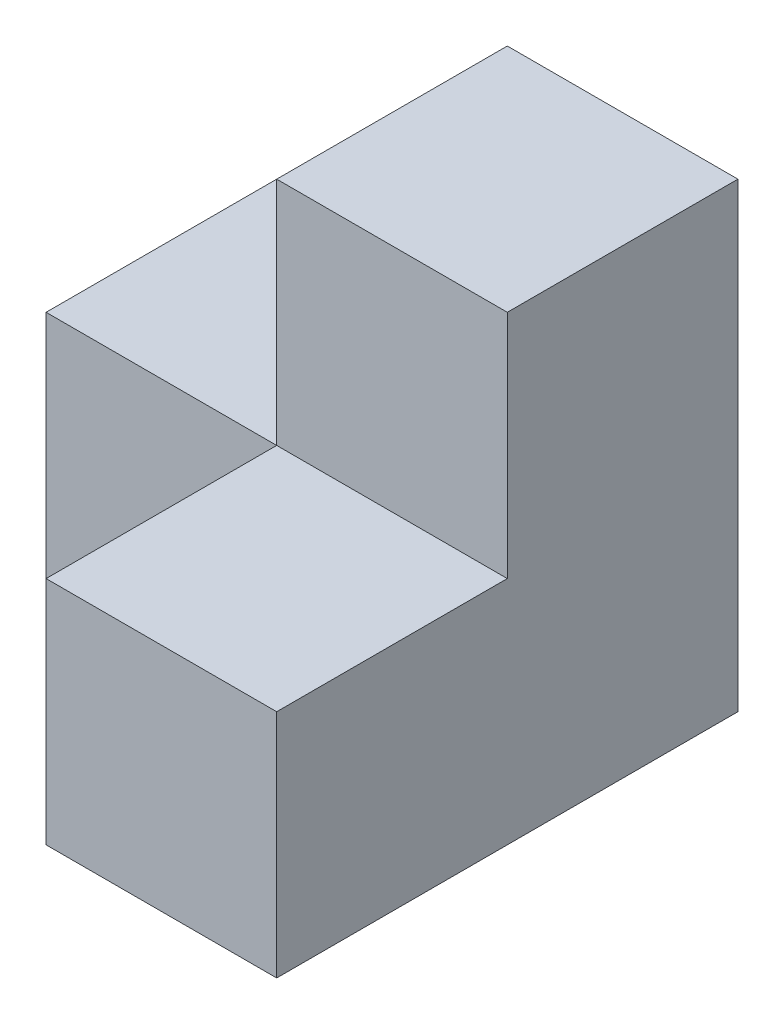
SolidWorks part; units mm, degrees
ref_plane "Front Plane" through (0, 0, 0) normal (0, 0, 1) x (1, 0, 0)
ref_plane "Top Plane" through (0, 0, 0) normal (0, 1, 0) x (1, 0, 0)
ref_plane "Right Plane" through (0, 0, 0) normal (1, 0, 0) x (0, 0, -1)
sketch "Sketch1" plane through (0, 0, 0) normal (0, 1, 0) x (1, 0, 0)
  line L1 (-25.4, -25.4) -> (25.4, -25.4)
  line L2 (-25.4, -25.4) -> (-25.4, 25.4)
  line L3 (-25.4, 25.4) -> (25.4, 25.4)
  line L4 (25.4, -25.4) -> (25.4, 25.4)
  line L5 (-25.4, -25.4) -> (25.4, 25.4) construction
  line L6 (-25.4, 25.4) -> (25.4, -25.4) construction
  point P0 (0, 0)
  dimension "D1" = 50.8
  dimension "D2" = 50.8
extrude "Boss-Extrude1" add sketch "Sketch1" along normal blind 25.4
sketch "Sketch2" plane through (0, 25.4, 0) normal (0, 1, 0) x (1, 0, 0)
  line L1 (-25.4, -25.4) -> (0, -25.4)
  line L2 (-25.4, -25.4) -> (-25.4, 0)
  line L3 (-25.4, 0) -> (0, 0)
  line L4 (0, -25.4) -> (0, 0)
extrude "Cut-Extrude1" cut sketch "Sketch2" against normal through all
sketch "Sketch3" plane through (0, 25.4, 0) normal (0, 1, 0) x (1, 0, 0)
  line L1 (25.4, 25.4) -> (0, 25.4)
  line L2 (25.4, 25.4) -> (25.4, 0)
  line L3 (25.4, 0) -> (0, 0)
  line L4 (0, 25.4) -> (0, 0)
  line L6 (-25.4, 25.4) -> (-25.4, 0)
  line L7 (-25.4, 0) -> (0, 0)
  line L8 (0, 0) -> (0, -25.4)
  line L9 (0, -25.4) -> (25.4, -25.4)
  line L10 (25.4, -25.4) -> (25.4, 25.4)
  line L11 (25.4, 25.4) -> (-25.4, 25.4)
  line L12 (-25.4, 25.4) -> (-25.4, 0)
  line L13 (-25.4, 0) -> (0, 0)
  line L14 (0, 0) -> (0, -25.4)
  line L15 (0, -25.4) -> (25.4, -25.4)
  line L16 (25.4, -25.4) -> (25.4, 25.4)
  line L17 (25.4, 25.4) -> (-25.4, 25.4)
  line M11 (25.4, -25.4) -> (25.4, 25.4)
  line M12 (25.4, 25.4) -> (-25.4, 25.4)
  dimension "D1" = 0
extrude "Boss-Extrude2" add sketch "Sketch3" along normal blind 25.4 contours L4 L3 M12 M11
